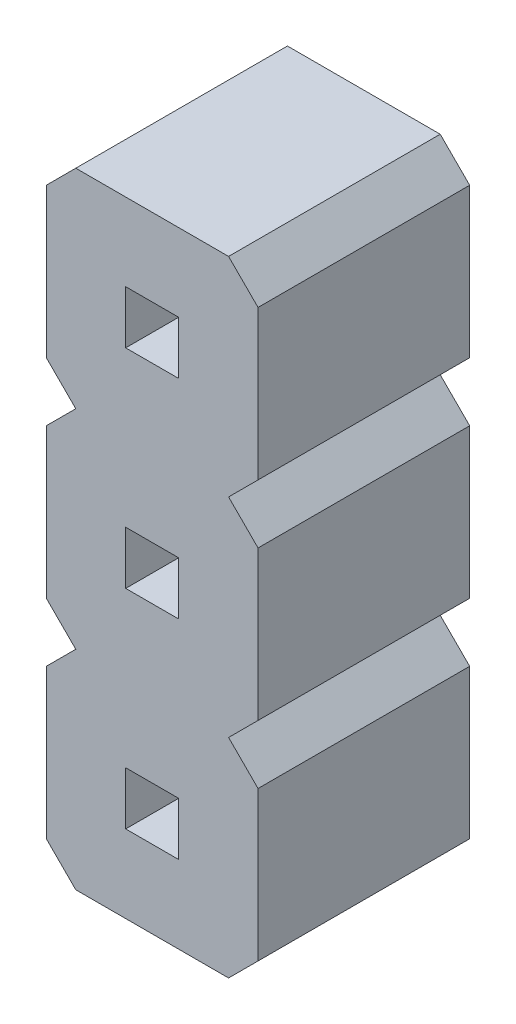
SolidWorks part; units mm, degrees
ref_plane "Alzado" through (0, 0, 0) normal (0, 0, 1) x (1, 0, 0)
ref_plane "Planta" through (0, 0, 0) normal (0, 1, 0) x (1, 0, 0)
ref_plane "Vista lateral" through (0, 0, 0) normal (1, 0, 0) x (0, 0, -1)
sketch "pin_drawing" plane through (0, 0, 0) normal (0, 0, 1) x (1, 0, 0)
  line L0 (0.9525, -0.932) -> (0, -0.932) construction
  line L1 (0, 2.1464) -> (0, 0.3536)
  line L2 (0, -0.3536) -> (0, -2.1464)
  line L3 (0, -0.3536) -> (0.3536, 0)
  line L4 (1.5885, -1.568) -> (2.541, -1.568) construction
  line L5 (0, 2.1464) -> (0.3536, 2.5)
  line L6 (2.541, -0.3536) -> (2.541, -2.1464)
  line L7 (0.9525, -1.25) -> (0.9525, -0.932) construction
  line L8 (2.541, -2.1464) -> (2.1874, -2.5)
  line L9 (2.1874, 0) -> (2.541, -0.3536)
  line L10 (1.5885, -1.25) -> (1.5885, -1.568) construction
  line L11 (0.3536, -2.5) -> (0, -2.1464)
  line L12 (0.9525, -0.932) -> (1.5885, -0.932)
  line L13 (0.9525, -0.932) -> (0.9525, -1.568)
  line L14 (0.9525, -1.568) -> (1.5885, -1.568)
  line L15 (1.5885, -0.932) -> (1.5885, -1.568)
  line L16 (2.541, 2.1464) -> (2.541, 0.3536)
  line L17 (2.541, 0.3536) -> (2.1874, 0)
  line L18 (2.1874, 2.5) -> (2.541, 2.1464)
  line L19 (0.3536, 0) -> (0, 0.3536)
  line L20 (0.9525, 1.568) -> (1.5885, 1.568)
  line L21 (0.9525, 1.568) -> (0.9525, 0.932)
  line L22 (0.9525, 0.932) -> (1.5885, 0.932)
  line L23 (1.5885, 1.568) -> (1.5885, 0.932)
  line L24 (0.9525, 1.568) -> (0, 1.568) construction
  line L25 (1.5885, 0.932) -> (2.541, 0.932) construction
  line L26 (0.9525, 1.25) -> (0.9525, 1.568) construction
  line L27 (1.5885, 1.25) -> (1.5885, 0.932) construction
  line L28 (0, 4.6464) -> (0, 2.8536)
  line L29 (0, 4.6464) -> (0.3536, 5)
  line L30 (2.541, 4.6464) -> (2.541, 2.8536)
  line L31 (2.541, 2.8536) -> (2.1874, 2.5)
  line L32 (2.1874, 5) -> (2.541, 4.6464)
  line L33 (0.3536, 2.5) -> (0, 2.8536)
  line L34 (0.9525, 4.068) -> (1.5885, 4.068)
  line L35 (0.9525, 4.068) -> (0.9525, 3.432)
  line L36 (0.9525, 3.432) -> (1.5885, 3.432)
  line L37 (1.5885, 4.068) -> (1.5885, 3.432)
  line L38 (0.9525, 4.068) -> (0, 4.068) construction
  line L39 (1.5885, 3.432) -> (2.541, 3.432) construction
  line L40 (0.9525, 3.75) -> (0.9525, 4.068) construction
  line L41 (1.5885, 3.75) -> (1.5885, 3.432) construction
  line L42 (0, 7.1464) -> (0, 5.3536) construction
  line L43 (0, 7.1464) -> (0.3536, 7.5) construction
  line L44 (2.541, 7.1464) -> (2.541, 5.3536) construction
  line L45 (2.541, 5.3536) -> (2.1874, 5) construction
  line L46 (2.1874, 7.5) -> (2.541, 7.1464) construction
  line L47 (0.3536, 5) -> (0, 5.3536) construction
  line L48 (0.9525, 6.568) -> (1.5885, 6.568) construction
  line L49 (0.9525, 6.568) -> (0.9525, 5.932) construction
  line L50 (0.9525, 5.932) -> (1.5885, 5.932) construction
  line L51 (1.5885, 6.568) -> (1.5885, 5.932) construction
  line L52 (0.9525, 6.568) -> (0, 6.568) construction
  line L53 (1.5885, 5.932) -> (2.541, 5.932) construction
  line L54 (0.9525, 6.25) -> (0.9525, 6.568) construction
  line L55 (1.5885, 6.25) -> (1.5885, 5.932) construction
  line L56 (0, 9.6464) -> (0, 7.8536) construction
  line L57 (0, 9.6464) -> (0.3536, 10) construction
  line L58 (2.541, 9.6464) -> (2.541, 7.8536) construction
  line L59 (2.541, 7.8536) -> (2.1874, 7.5) construction
  line L60 (2.1874, 10) -> (2.541, 9.6464) construction
  line L61 (0.3536, 7.5) -> (0, 7.8536) construction
  line L62 (0.9525, 9.068) -> (1.5885, 9.068) construction
  line L63 (0.9525, 9.068) -> (0.9525, 8.432) construction
  line L64 (0.9525, 8.432) -> (1.5885, 8.432) construction
  line L65 (1.5885, 9.068) -> (1.5885, 8.432) construction
  line L66 (0.9525, 9.068) -> (0, 9.068) construction
  line L67 (1.5885, 8.432) -> (2.541, 8.432) construction
  line L68 (0.9525, 8.75) -> (0.9525, 9.068) construction
  line L69 (1.5885, 8.75) -> (1.5885, 8.432) construction
  line L70 (0, 12.1464) -> (0, 10.3536) construction
  line L71 (0, 12.1464) -> (0.3536, 12.5) construction
  line L72 (2.541, 12.1464) -> (2.541, 10.3536) construction
  line L73 (2.541, 10.3536) -> (2.1874, 10) construction
  line L74 (2.1874, 12.5) -> (2.541, 12.1464) construction
  line L75 (0.3536, 10) -> (0, 10.3536) construction
  line L76 (0.9525, 11.568) -> (1.5885, 11.568) construction
  line L77 (0.9525, 11.568) -> (0.9525, 10.932) construction
  line L78 (0.9525, 10.932) -> (1.5885, 10.932) construction
  line L79 (1.5885, 11.568) -> (1.5885, 10.932) construction
  line L80 (0.9525, 11.568) -> (0, 11.568) construction
  line L81 (1.5885, 10.932) -> (2.541, 10.932) construction
  line L82 (0.9525, 11.25) -> (0.9525, 11.568) construction
  line L83 (1.5885, 11.25) -> (1.5885, 10.932) construction
  line L84 (0, 14.6464) -> (0, 12.8536) construction
  line L85 (0, 14.6464) -> (0.3536, 15) construction
  line L86 (2.541, 14.6464) -> (2.541, 12.8536) construction
  line L87 (2.541, 12.8536) -> (2.1874, 12.5) construction
  line L88 (2.1874, 15) -> (2.541, 14.6464) construction
  line L89 (0.3536, 12.5) -> (0, 12.8536) construction
  line L90 (0.9525, 14.068) -> (1.5885, 14.068) construction
  line L91 (0.9525, 14.068) -> (0.9525, 13.432) construction
  line L92 (0.9525, 13.432) -> (1.5885, 13.432) construction
  line L93 (1.5885, 14.068) -> (1.5885, 13.432) construction
  line L94 (0.9525, 14.068) -> (0, 14.068) construction
  line L95 (1.5885, 13.432) -> (2.541, 13.432) construction
  line L96 (0.9525, 13.75) -> (0.9525, 14.068) construction
  line L97 (1.5885, 13.75) -> (1.5885, 13.432) construction
  line L98 (0, 17.1464) -> (0, 15.3536) construction
  line L99 (0, 17.1464) -> (0.3536, 17.5) construction
  line L100 (2.541, 17.1464) -> (2.541, 15.3536) construction
  line L101 (2.541, 15.3536) -> (2.1874, 15) construction
  line L102 (2.1874, 17.5) -> (2.541, 17.1464) construction
  line L103 (0.3536, 15) -> (0, 15.3536) construction
  line L104 (0.9525, 16.568) -> (1.5885, 16.568) construction
  line L105 (0.9525, 16.568) -> (0.9525, 15.932) construction
  line L106 (0.9525, 15.932) -> (1.5885, 15.932) construction
  line L107 (1.5885, 16.568) -> (1.5885, 15.932) construction
  line L108 (0.9525, 16.568) -> (0, 16.568) construction
  line L109 (1.5885, 15.932) -> (2.541, 15.932) construction
  line L110 (0.9525, 16.25) -> (0.9525, 16.568) construction
  line L111 (1.5885, 16.25) -> (1.5885, 15.932) construction
  line L112 (0, 19.6464) -> (0, 17.8536) construction
  line L113 (0, 19.6464) -> (0.3536, 20) construction
  line L114 (2.541, 19.6464) -> (2.541, 17.8536) construction
  line L115 (2.541, 17.8536) -> (2.1874, 17.5) construction
  line L116 (2.1874, 20) -> (2.541, 19.6464) construction
  line L117 (0.3536, 17.5) -> (0, 17.8536) construction
  line L118 (0.9525, 19.068) -> (1.5885, 19.068) construction
  line L119 (0.9525, 19.068) -> (0.9525, 18.432) construction
  line L120 (0.9525, 18.432) -> (1.5885, 18.432) construction
  line L121 (1.5885, 19.068) -> (1.5885, 18.432) construction
  line L122 (0.9525, 19.068) -> (0, 19.068) construction
  line L123 (1.5885, 18.432) -> (2.541, 18.432) construction
  line L124 (0.9525, 18.75) -> (0.9525, 19.068) construction
  line L125 (1.5885, 18.75) -> (1.5885, 18.432) construction
  line L126 (0, 22.1464) -> (0, 20.3536) construction
  line L127 (0, 22.1464) -> (0.3536, 22.5) construction
  line L128 (2.541, 22.1464) -> (2.541, 20.3536) construction
  line L129 (2.541, 20.3536) -> (2.1874, 20) construction
  line L130 (2.1874, 22.5) -> (2.541, 22.1464) construction
  line L131 (0.3536, 20) -> (0, 20.3536) construction
  line L132 (0.9525, 21.568) -> (1.5885, 21.568) construction
  line L133 (0.9525, 21.568) -> (0.9525, 20.932) construction
  line L134 (0.9525, 20.932) -> (1.5885, 20.932) construction
  line L135 (1.5885, 21.568) -> (1.5885, 20.932) construction
  line L136 (0.9525, 21.568) -> (0, 21.568) construction
  line L137 (1.5885, 20.932) -> (2.541, 20.932) construction
  line L138 (0.9525, 21.25) -> (0.9525, 21.568) construction
  line L139 (1.5885, 21.25) -> (1.5885, 20.932) construction
  line L140 (0, 24.6464) -> (0, 22.8536) construction
  line L141 (0, 24.6464) -> (0.3536, 25) construction
  line L142 (2.541, 24.6464) -> (2.541, 22.8536) construction
  line L143 (2.541, 22.8536) -> (2.1874, 22.5) construction
  line L144 (2.1874, 25) -> (2.541, 24.6464) construction
  line L145 (0.3536, 22.5) -> (0, 22.8536) construction
  line L146 (0.9525, 24.068) -> (1.5885, 24.068) construction
  line L147 (0.9525, 24.068) -> (0.9525, 23.432) construction
  line L148 (0.9525, 23.432) -> (1.5885, 23.432) construction
  line L149 (1.5885, 24.068) -> (1.5885, 23.432) construction
  line L150 (0.9525, 24.068) -> (0, 24.068) construction
  line L151 (1.5885, 23.432) -> (2.541, 23.432) construction
  line L152 (0.9525, 23.75) -> (0.9525, 24.068) construction
  line L153 (1.5885, 23.75) -> (1.5885, 23.432) construction
  line L154 (0, 27.1464) -> (0, 25.3536) construction
  line L155 (0, 27.1464) -> (0.3536, 27.5) construction
  line L156 (2.541, 27.1464) -> (2.541, 25.3536) construction
  line L157 (2.541, 25.3536) -> (2.1874, 25) construction
  line L158 (2.1874, 27.5) -> (2.541, 27.1464) construction
  line L159 (0.3536, 25) -> (0, 25.3536) construction
  line L160 (0.9525, 26.568) -> (1.5885, 26.568) construction
  line L161 (0.9525, 26.568) -> (0.9525, 25.932) construction
  line L162 (0.9525, 25.932) -> (1.5885, 25.932) construction
  line L163 (1.5885, 26.568) -> (1.5885, 25.932) construction
  line L164 (0.9525, 26.568) -> (0, 26.568) construction
  line L165 (1.5885, 25.932) -> (2.541, 25.932) construction
  line L166 (0.9525, 26.25) -> (0.9525, 26.568) construction
  line L167 (1.5885, 26.25) -> (1.5885, 25.932) construction
  line L168 (2.1874, -2.5) -> (0.3536, -2.5)
  line L169 (0.3536, 27.5) -> (2.1874, 27.5) construction
  line L170 (0.3536, 5) -> (2.1874, 5)
  dimension "D1" = 0.318
  dimension "D2" = 0.9525
  dimension "D3" = 0.5
  dimension "D4" = 135
  dimension "D5" = 0.5
  dimension "D6" = 135
  dimension "D7" = 12
extrude "Boss-Extrude1" add sketch "pin_drawing" along normal blind 2.54
